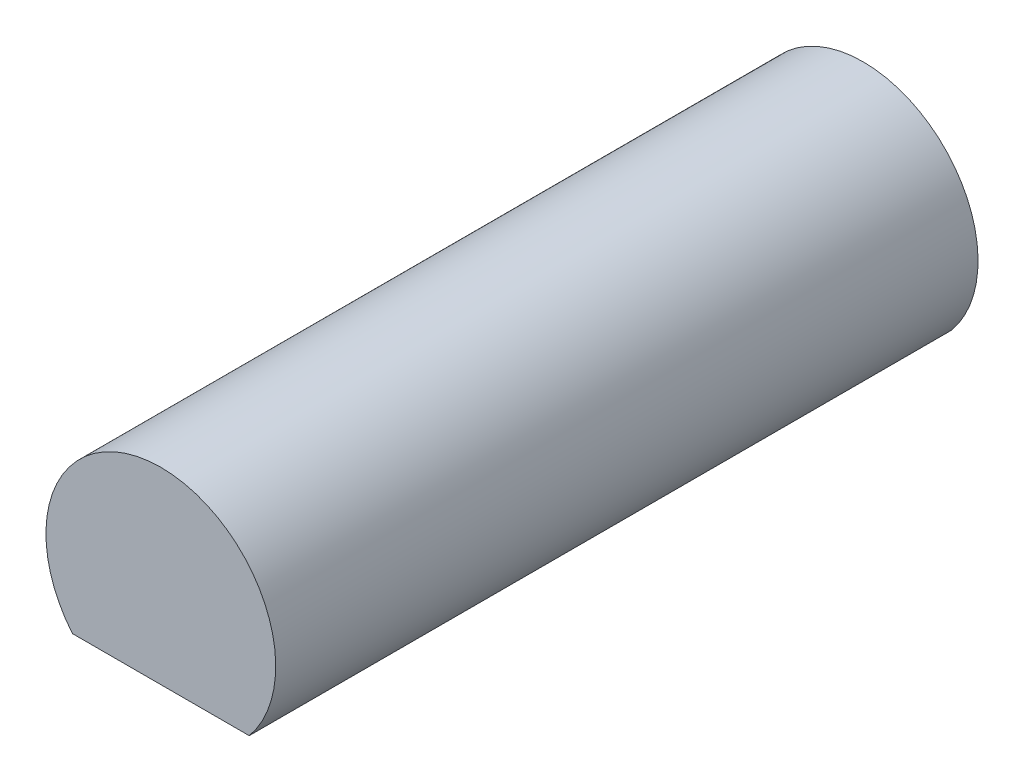
SolidWorks part; units mm, degrees
ref_plane "Plan de face" through (0, 0, 0) normal (0, 0, 1) x (1, 0, 0)
ref_plane "Plan de dessus" through (0, 0, 0) normal (0, 1, 0) x (1, 0, 0)
ref_plane "Plan de droite" through (0, 0, 0) normal (1, 0, 0) x (0, 0, -1)
sketch "Esquisse1" plane through (0, 0, 0) normal (0, 0, 1) x (1, 0, 0)
  line L1 (0, -0.955) -> (1.1502, -0.955)
  line L2 (0, -0.955) -> (-1.1502, -0.955)
  arc A0 (1.1502, -0.955) -> (-1.1502, -0.955) centre (0, 0) ccw
  dimension "D1" = 2.99
extrude "Boss.-Extru.1" add sketch "Esquisse1" along normal blind 9.14
